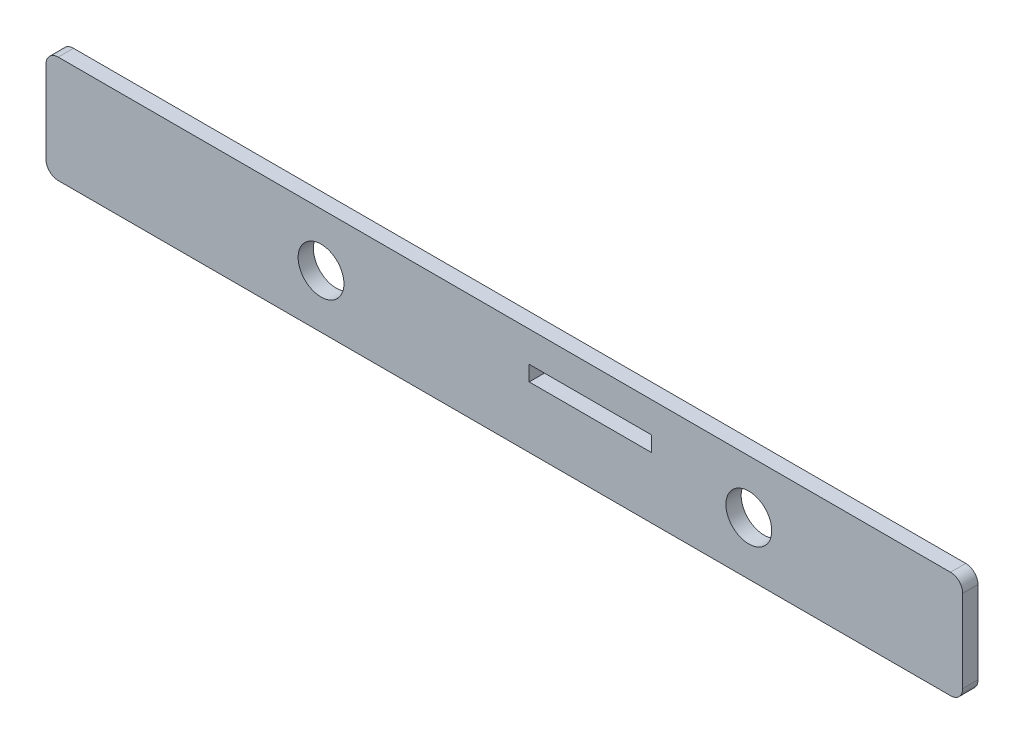
SolidWorks part; units mm, degrees
material "Plywood"
ref_plane "Front Plane" through (0, 0, 0) normal (0, 0, 1) x (1, 0, 0)
ref_plane "Top Plane" through (0, 0, 0) normal (0, 1, 0) x (1, 0, 0)
ref_plane "Right Plane" through (0, 0, 0) normal (1, 0, 0) x (0, 0, -1)
sketch "Sketch1" plane through (0, 0, 0) normal (0, 0, 1) x (1, 0, 0)
  line L1 (1104.9, -28.575) -> (1485.9, -28.575)
  line L2 (1104.9, -28.575) -> (1104.9, -73.025)
  line L3 (1104.9, -73.025) -> (1485.9, -73.025)
  line L4 (1485.9, -28.575) -> (1485.9, -73.025)
  circle A0 centre (1219.2, -50.8) radius 9.525
  circle A1 centre (1397, -50.8) radius 9.525
  point P11 (1104.9, -50.8)
  dimension "D4" = 19.05
  dimension "D6" = 1219.2
  dimension "D7" = 1397
  dimension "D1" = 44.45
  dimension "D2" = 1104.9
  dimension "D3" = 1485.9
  dimension "D5" = 73.025
extrude "Boss-Extrude1" add sketch "Sketch1" along normal blind 6.35
fillet "Fillet1" radius 5.08 4 edges at (1485.9, -73.025, 3.175) (1485.9, -28.575, 3.175) (1104.9, -73.025, 3.175) (1104.9, -28.575, 3.175)
sketch "Sketch2" plane through (0, 0, 6.35) normal (0, 0, 1) x (1, 0, 0)
  line L0 (1109.98, -73.025) -> (1480.82, -73.025) construction
  line L1 (1480.82, -28.575) -> (1109.98, -28.575) construction
  line L2 (1109.98, -73.025) -> (1480.82, -73.025)
  line L3 (1480.82, -28.575) -> (1109.98, -28.575)
  line L4 (1300.1625, -28.575) -> (1300.1625, -73.025)
  line L5 (1362.075, -28.575) -> (1362.075, -73.025)
  line L7 (1305.7188, -41.275) -> (1356.5187, -41.275)
  line L8 (1305.7188, -41.275) -> (1305.7188, -47.625)
  line L9 (1305.7188, -47.625) -> (1356.5187, -47.625)
  line L10 (1356.5187, -41.275) -> (1356.5187, -47.625)
  circle A0 centre (1397, -50.8) radius 9.525 construction
  circle A1 centre (1397, -50.8) radius 9.525
  dimension "D1" = 96.8375
  dimension "D2" = 34.925
  dimension "D3" = 61.9125
  dimension "D4" = 50.8
  dimension "D5" = 25.4
  dimension "D6" = 6.35
  dimension "D7" = 5.5562
extrude "Cut-Extrude1" cut sketch "Sketch2" against normal through all contours L10 L7 L8 L9
equation "\"D7@Sketch2\"=(\"D3@Sketch2\"-\"D4@Sketch2\")/2"
